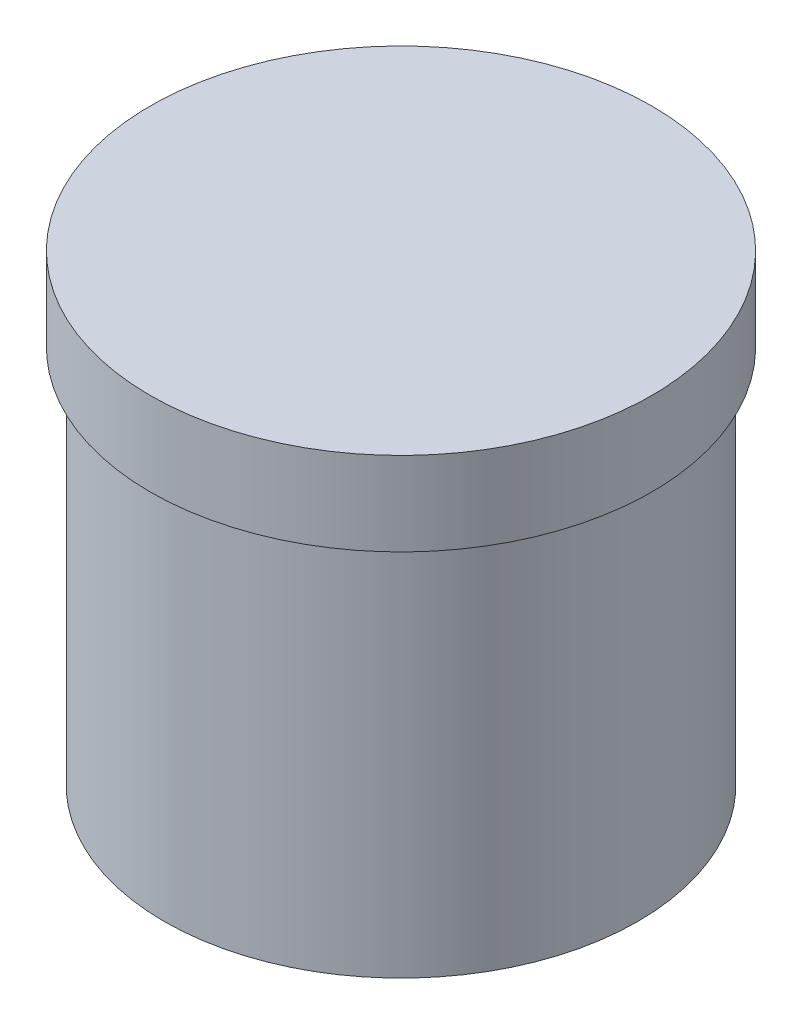
SolidWorks part; units mm, degrees
ref_plane "Front Plane" through (0, 0, 0) normal (0, 0, 1) x (1, 0, 0)
ref_plane "Top Plane" through (0, 0, 0) normal (0, 1, 0) x (1, 0, 0)
ref_plane "Right Plane" through (0, 0, 0) normal (1, 0, 0) x (0, 0, -1)
sketch "Sketch1" plane through (0, 0, 0) normal (0, 1, 0) x (1, 0, 0)
  circle A0 centre (0, 0) radius 42.5
  dimension "D1" = 85
extrude "Boss-Extrude1" add sketch "Sketch1" along normal blind 68
sketch "Sketch2" plane through (0, 68, 0) normal (0, 1, 0) x (1, 0, 0)
  circle A0 centre (0, 0) radius 45
  dimension "D1" = 90
extrude "Boss-Extrude2" add sketch "Sketch2" along normal blind 15
